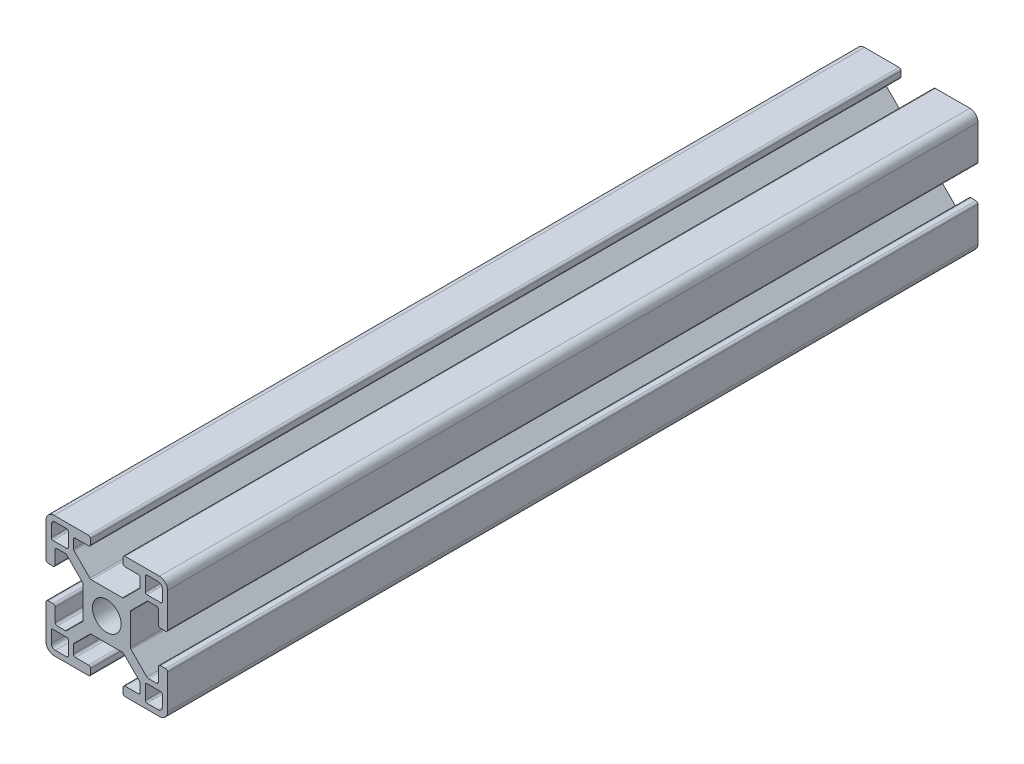
SolidWorks part; units mm, degrees
ref_plane "Front Plane" through (0, 0, 0) normal (0, 0, 1) x (1, 0, 0)
ref_plane "Top Plane" through (0, 0, 0) normal (0, 1, 0) x (1, 0, 0)
ref_plane "Right Plane" through (0, 0, 0) normal (1, 0, 0) x (0, 0, -1)
sketch "Sketch1" plane through (0, 0, 0) normal (0, 0, 1) x (1, 0, 0)
  line L0 (3.9799, -2.4733) -> (3.1981, -1.4942) construction
  line L1 (1.4942, -3.1981) -> (2.4733, -3.9799) construction
  line L2 (-2.4733, -3.9799) -> (-1.4942, -3.1981) construction
  line L3 (-3.1981, -1.4942) -> (-3.9799, -2.4733) construction
  line L4 (-3.9799, 2.4733) -> (-3.1981, 1.4942) construction
  line L5 (-1.4942, 3.1981) -> (-2.4733, 3.9799) construction
  line L6 (2.4733, 3.9799) -> (1.4942, 3.1981) construction
  line L7 (3.1981, 1.4942) -> (3.9799, 2.4733) construction
  line L8 (-12.6999, -13.6999) -> (-9.881, -13.6999)
  line L9 (-13.6999, -9.881) -> (-13.6999, -12.6999)
  line L10 (-9.88, -9.5) -> (-13.3189, -9.5)
  line L11 (-9.5, -13.3189) -> (-9.5, -9.88)
  line L12 (13.6999, -12.6999) -> (13.6999, -9.881)
  line L13 (9.881, -13.6999) -> (12.6999, -13.6999)
  line L14 (9.5, -9.88) -> (9.5, -13.3189)
  line L15 (13.3189, -9.5) -> (9.88, -9.5)
  line L16 (9.88, 9.5) -> (13.3189, 9.5)
  line L17 (9.5, 13.3189) -> (9.5, 9.88)
  line L18 (12.6999, 13.6999) -> (9.881, 13.6999)
  line L19 (13.6999, 9.881) -> (13.6999, 12.6999)
  line L20 (-13.6999, 12.6999) -> (-13.6999, 9.881)
  line L21 (-9.881, 13.6999) -> (-12.6999, 13.6999)
  line L22 (-9.5, 9.88) -> (-9.5, 13.3189)
  line L23 (-13.3189, 9.5) -> (-9.88, 9.5)
  line L24 (14.4999, -4) -> (13.2425, -4)
  line L25 (12.7425, -4.5) -> (12.7425, -7.7325)
  line L26 (12.2428, -8.25) -> (10.2602, -8.25)
  line L27 (9.9066, -8.1035) -> (5.9811, -4.178)
  line L28 (5.8347, -3.8245) -> (5.8347, -1.0125)
  line L29 (5.8347, -1.0125) -> (5.3247, -0.0625) construction
  line L30 (5.3247, -0.0625) -> (5.8347, 0.8875) construction
  line L31 (5.8347, 0.8875) -> (5.8347, 3.8245)
  line L32 (5.9811, 4.178) -> (9.9066, 8.1035)
  line L33 (10.2602, 8.25) -> (12.2428, 8.25)
  line L34 (12.7425, 7.7325) -> (12.7425, 4.5)
  line L35 (13.2425, 4) -> (14.4999, 4)
  line L36 (14.9999, 4.5) -> (14.9999, 12.9999)
  line L37 (12.9999, 14.9999) -> (4.5, 14.9999)
  line L38 (4, 14.4999) -> (4, 13.2425)
  line L39 (4.5, 12.7425) -> (7.7325, 12.7425)
  line L40 (8.25, 12.2428) -> (8.25, 10.2602)
  line L41 (8.1035, 9.9066) -> (4.178, 5.9811)
  line L42 (3.8245, 5.8347) -> (0.95, 5.8347)
  line L43 (0.95, 5.8347) -> (0, 5.3247) construction
  line L44 (0, 5.3247) -> (-0.95, 5.8347) construction
  line L45 (-0.95, 5.8347) -> (-3.8245, 5.8347)
  line L46 (-4.178, 5.9811) -> (-8.1035, 9.9066)
  line L47 (-8.25, 10.2602) -> (-8.25, 12.2428)
  line L48 (-7.7325, 12.7425) -> (-4.5, 12.7425)
  line L49 (-4, 13.2425) -> (-4, 14.4999)
  line L50 (-4.5, 14.9999) -> (-12.9999, 14.9999)
  line L51 (-14.9999, 12.9999) -> (-14.9999, 4.5)
  line L52 (-14.4999, 4) -> (-13.2425, 4)
  line L53 (-12.7425, 4.5) -> (-12.7425, 7.7325)
  line L54 (-12.2428, 8.25) -> (-10.2602, 8.25)
  line L55 (-9.9066, 8.1035) -> (-5.9811, 4.178)
  line L56 (-5.8347, 3.8245) -> (-5.8347, 0.8875)
  line L57 (-5.8347, 0.8875) -> (-5.3247, -0.0625) construction
  line L58 (-5.3247, -0.0625) -> (-5.8347, -1.0125) construction
  line L59 (-5.8347, -1.0125) -> (-5.8347, -3.8245)
  line L60 (-5.9811, -4.178) -> (-9.9066, -8.1035)
  line L61 (-10.2602, -8.25) -> (-12.2428, -8.25)
  line L62 (-12.7425, -7.7325) -> (-12.7425, -4.5)
  line L63 (-13.2425, -4) -> (-14.4999, -4)
  line L64 (-14.9999, -4.5) -> (-14.9999, -12.9999)
  line L65 (-12.9999, -14.9999) -> (-4.5, -14.9999)
  line L66 (-4, -14.4999) -> (-4, -13.2425)
  line L67 (-4.5, -12.7425) -> (-7.7325, -12.7425)
  line L68 (-8.25, -12.2428) -> (-8.25, -10.2602)
  line L69 (-8.1035, -9.9066) -> (-4.178, -5.9811)
  line L70 (-3.8245, -5.8347) -> (-0.95, -5.8347)
  line L71 (-0.95, -5.8347) -> (0, -5.3247) construction
  line L72 (0, -5.3247) -> (0.95, -5.8347) construction
  line L73 (0.95, -5.8347) -> (3.8245, -5.8347)
  line L74 (4.178, -5.9811) -> (8.1035, -9.9066)
  line L75 (8.25, -10.2602) -> (8.25, -12.2428)
  line L76 (7.7325, -12.7425) -> (4.5, -12.7425)
  line L77 (4, -13.2425) -> (4, -14.4999)
  line L78 (4.5, -14.9999) -> (12.9999, -14.9999)
  line L79 (14.9999, -12.9999) -> (14.9999, -4.5)
  line L80 (-5.8347, -1.0125) -> (-5.8347, 0.8875)
  line L81 (-0.95, 5.8347) -> (0.95, 5.8347)
  line L82 (5.8347, 0.8875) -> (5.8347, -1.0125)
  line L83 (-0.95, -5.8347) -> (0.95, -5.8347)
  arc A0 (2.4733, -3.9799) -> (3.9799, -2.4733) centre (3.1422, -3.1422) ccw construction
  arc A1 (-1.4942, -3.1981) -> (1.4942, -3.1981) centre (0, 0) ccw construction
  arc A2 (-3.9799, -2.4733) -> (-2.4733, -3.9799) centre (-3.1422, -3.1422) ccw construction
  arc A3 (-3.1981, 1.4942) -> (-3.1981, -1.4942) centre (0, 0) ccw construction
  arc A4 (-2.4733, 3.9799) -> (-3.9799, 2.4733) centre (-3.1422, 3.1422) ccw construction
  arc A5 (1.4942, 3.1981) -> (-1.4942, 3.1981) centre (0, 0) ccw construction
  arc A6 (3.9799, 2.4733) -> (2.4733, 3.9799) centre (3.1422, 3.1422) ccw construction
  arc A7 (3.1981, -1.4942) -> (3.1981, 1.4942) centre (0, 0) ccw construction
  arc A8 (-13.6999, -12.6999) -> (-12.6999, -13.6999) centre (-12.6999, -12.6999) ccw
  arc A9 (-13.3189, -9.5) -> (-13.6999, -9.881) centre (-13.3189, -9.881) ccw
  arc A10 (-9.5, -9.88) -> (-9.88, -9.5) centre (-9.88, -9.88) ccw
  arc A11 (-9.881, -13.6999) -> (-9.5, -13.3189) centre (-9.881, -13.3189) ccw
  arc A12 (12.6999, -13.6999) -> (13.6999, -12.6999) centre (12.6999, -12.6999) ccw
  arc A13 (9.5, -13.3189) -> (9.881, -13.6999) centre (9.881, -13.3189) ccw
  arc A14 (9.88, -9.5) -> (9.5, -9.88) centre (9.88, -9.88) ccw
  arc A15 (13.6999, -9.881) -> (13.3189, -9.5) centre (13.3189, -9.881) ccw
  arc A16 (9.5, 9.88) -> (9.88, 9.5) centre (9.88, 9.88) ccw
  arc A17 (9.881, 13.6999) -> (9.5, 13.3189) centre (9.881, 13.3189) ccw
  arc A18 (13.6999, 12.6999) -> (12.6999, 13.6999) centre (12.6999, 12.6999) ccw
  arc A19 (13.3189, 9.5) -> (13.6999, 9.881) centre (13.3189, 9.881) ccw
  arc A20 (14.9999, -4.5) -> (14.4999, -4) centre (14.4999, -4.5) ccw
  arc A21 (13.2425, -4) -> (12.7425, -4.5) centre (13.2425, -4.5) ccw
  arc A22 (12.2428, -8.25) -> (12.7425, -7.7325) centre (12.2428, -7.75) ccw
  arc A23 (9.9066, -8.1035) -> (10.2602, -8.25) centre (10.2602, -7.75) ccw
  arc A24 (5.8347, -3.8245) -> (5.9811, -4.178) centre (6.3347, -3.8245) ccw
  arc A25 (5.9811, 4.178) -> (5.8347, 3.8245) centre (6.3347, 3.8245) ccw
  arc A26 (10.2602, 8.25) -> (9.9066, 8.1035) centre (10.2602, 7.75) ccw
  arc A27 (12.7425, 7.7325) -> (12.2428, 8.25) centre (12.2428, 7.75) ccw
  arc A28 (12.7425, 4.5) -> (13.2425, 4) centre (13.2425, 4.5) ccw
  arc A29 (14.4999, 4) -> (14.9999, 4.5) centre (14.4999, 4.5) ccw
  arc A30 (14.9999, 12.9999) -> (12.9999, 14.9999) centre (12.9999, 12.9999) ccw
  arc A31 (4.5, 14.9999) -> (4, 14.4999) centre (4.5, 14.4999) ccw
  arc A32 (4, 13.2425) -> (4.5, 12.7425) centre (4.5, 13.2425) ccw
  arc A33 (8.25, 12.2428) -> (7.7325, 12.7425) centre (7.75, 12.2428) ccw
  arc A34 (8.1035, 9.9066) -> (8.25, 10.2602) centre (7.75, 10.2602) ccw
  arc A35 (3.8245, 5.8347) -> (4.178, 5.9811) centre (3.8245, 6.3347) ccw
  arc A36 (-4.178, 5.9811) -> (-3.8245, 5.8347) centre (-3.8245, 6.3347) ccw
  arc A37 (-8.25, 10.2602) -> (-8.1035, 9.9066) centre (-7.75, 10.2602) ccw
  arc A38 (-7.7325, 12.7425) -> (-8.25, 12.2428) centre (-7.75, 12.2428) ccw
  arc A39 (-4.5, 12.7425) -> (-4, 13.2425) centre (-4.5, 13.2425) ccw
  arc A40 (-4, 14.4999) -> (-4.5, 14.9999) centre (-4.5, 14.4999) ccw
  arc A41 (-12.9999, 14.9999) -> (-14.9999, 12.9999) centre (-12.9999, 12.9999) ccw
  arc A42 (-14.9999, 4.5) -> (-14.4999, 4) centre (-14.4999, 4.5) ccw
  arc A43 (-13.2425, 4) -> (-12.7425, 4.5) centre (-13.2425, 4.5) ccw
  arc A44 (-12.2428, 8.25) -> (-12.7425, 7.7325) centre (-12.2428, 7.75) ccw
  arc A45 (-9.9066, 8.1035) -> (-10.2602, 8.25) centre (-10.2602, 7.75) ccw
  arc A46 (-5.8347, 3.8245) -> (-5.9811, 4.178) centre (-6.3347, 3.8245) ccw
  arc A47 (-5.9811, -4.178) -> (-5.8347, -3.8245) centre (-6.3347, -3.8245) ccw
  arc A48 (-10.2602, -8.25) -> (-9.9066, -8.1035) centre (-10.2602, -7.75) ccw
  arc A49 (-12.7425, -7.7325) -> (-12.2428, -8.25) centre (-12.2428, -7.75) ccw
  arc A50 (-12.7425, -4.5) -> (-13.2425, -4) centre (-13.2425, -4.5) ccw
  arc A51 (-14.4999, -4) -> (-14.9999, -4.5) centre (-14.4999, -4.5) ccw
  arc A52 (-14.9999, -12.9999) -> (-12.9999, -14.9999) centre (-12.9999, -12.9999) ccw
  arc A53 (-4.5, -14.9999) -> (-4, -14.4999) centre (-4.5, -14.4999) ccw
  arc A54 (-4, -13.2425) -> (-4.5, -12.7425) centre (-4.5, -13.2425) ccw
  arc A55 (-8.25, -12.2428) -> (-7.7325, -12.7425) centre (-7.75, -12.2428) ccw
  arc A56 (-8.1035, -9.9066) -> (-8.25, -10.2602) centre (-7.75, -10.2602) ccw
  arc A57 (-3.8245, -5.8347) -> (-4.178, -5.9811) centre (-3.8245, -6.3347) ccw
  arc A58 (4.178, -5.9811) -> (3.8245, -5.8347) centre (3.8245, -6.3347) ccw
  arc A59 (8.25, -10.2602) -> (8.1035, -9.9066) centre (7.75, -10.2602) ccw
  arc A60 (7.7325, -12.7425) -> (8.25, -12.2428) centre (7.75, -12.2428) ccw
  arc A61 (4.5, -12.7425) -> (4, -13.2425) centre (4.5, -13.2425) ccw
  arc A62 (4, -14.4999) -> (4.5, -14.9999) centre (4.5, -14.4999) ccw
  arc A63 (12.9999, -14.9999) -> (14.9999, -12.9999) centre (12.9999, -12.9999) ccw
  arc A64 (-12.6999, 13.6999) -> (-13.6999, 12.6999) centre (-12.6999, 12.6999) ccw
  arc A65 (-9.5, 13.3189) -> (-9.881, 13.6999) centre (-9.881, 13.3189) ccw
  arc A66 (-9.88, 9.5) -> (-9.5, 9.88) centre (-9.88, 9.88) ccw
  arc A67 (-13.6999, 9.881) -> (-13.3189, 9.5) centre (-13.3189, 9.881) ccw
  circle A68 centre (0, 0) radius 3.53
extrude "Boss-Extrude1" add sketch "Sketch1" along normal mid plane 200
